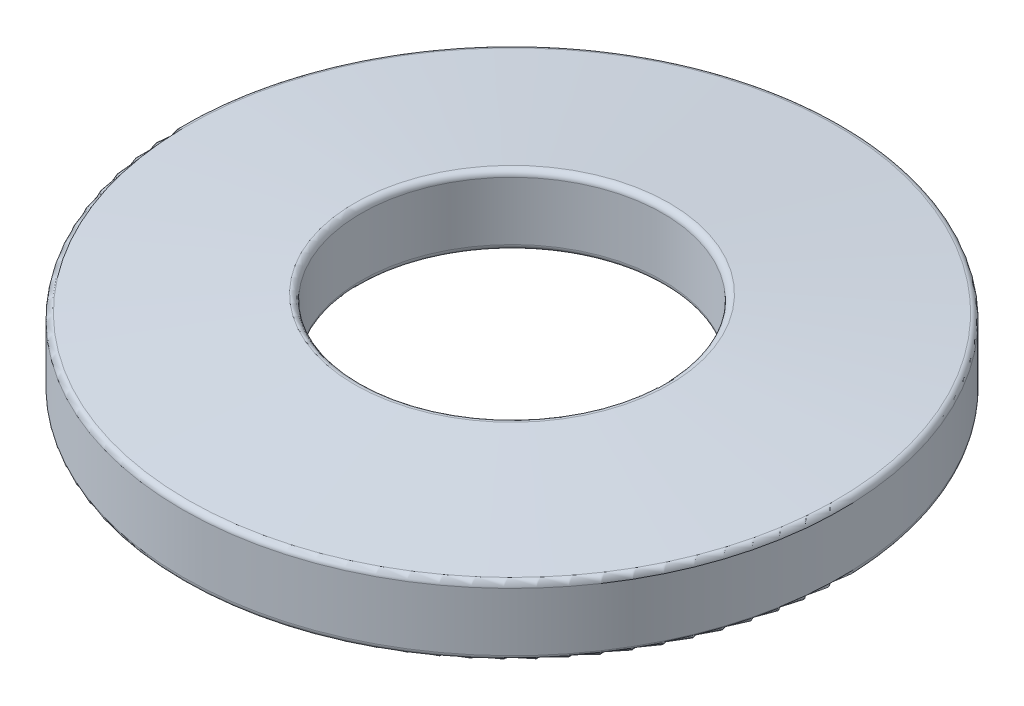
SolidWorks part; units mm, degrees
ref_plane "Front Plane" through (0, 0, 0) normal (0, 0, 1) x (1, 0, 0)
ref_plane "Top Plane" through (0, 0, 0) normal (0, 1, 0) x (1, 0, 0)
ref_plane "Right Plane" through (0, 0, 0) normal (1, 0, 0) x (0, 0, -1)
sketch "Sketch2" plane through (0, 0, 0) normal (1, 0, 0) x (0, 0, -1)
  line L0 (-6.5786, 0) -> (6.5786, 0) construction
  line L1 (6.5786, 3.81) -> (6.5786, 0.762)
  line L2 (6.5786, 0) -> (14.3637, 0) construction
  line L3 (6.5786, 0) -> (6.5786, 3.81) construction
  line L4 (6.5786, 3.81) -> (14.3637, 3.81) construction
  line L5 (14.3637, 0) -> (14.3637, 3.81) construction
  line L6 (14.3637, 0) -> (14.3637, 3.048)
  line L7 (6.5786, 3.81) -> (14.3637, 3.048)
  line L8 (14.3637, 0) -> (6.5786, 0.762)
  line L9 (0, 0) -> (0, 11.9435) construction
  point P4 (0, 0)
  dimension "D1" = 13.1572
  dimension "D2" = 14.3637
  dimension "D3" = 3.81
  dimension "D4" = 3.048
  dimension "D5" = 3.048
revolve "Revolve1" add sketch "Sketch2" angle 360 about L9
fillet "Fillet1" radius 0.254 4 edges at (0, 0, -14.3637) (0, 3.048, -14.3637) (0, 0.762, -6.5786) (0, 3.81, -6.5786)
